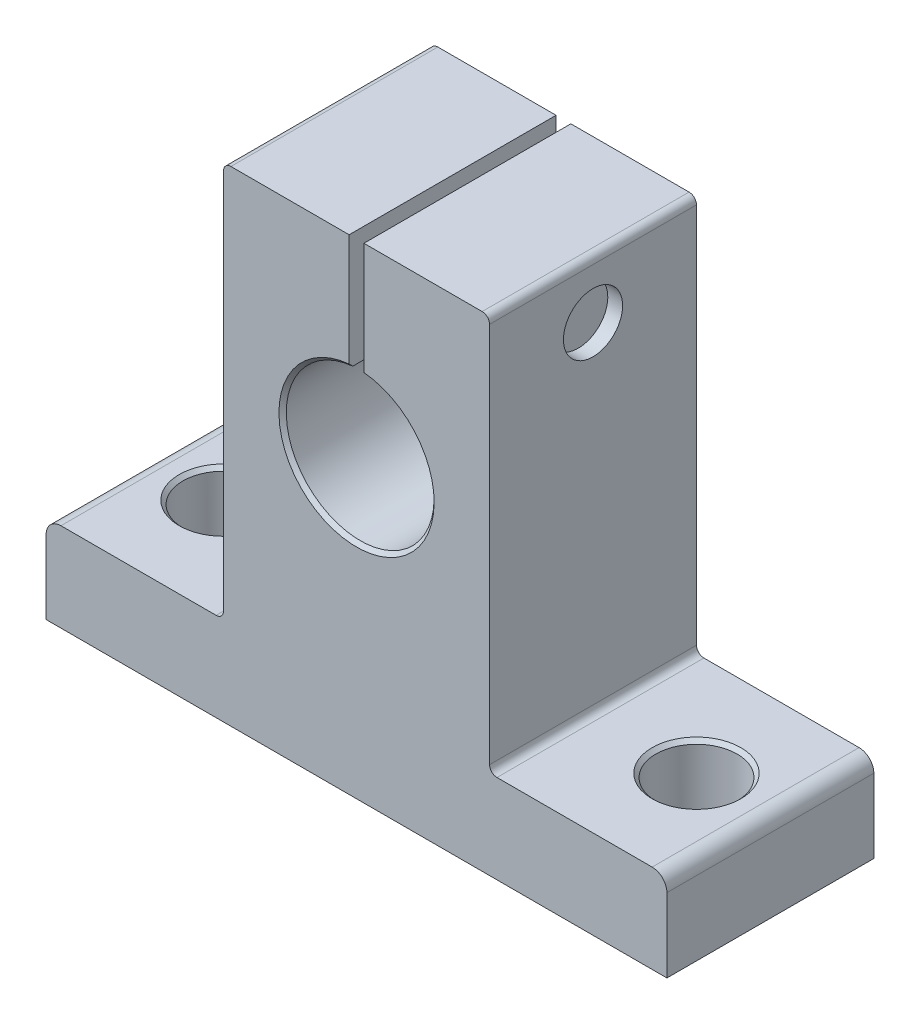
SolidWorks part; units mm, degrees
ref_plane "Front Plane" through (0, 0, 0) normal (0, 0, 1) x (1, 0, 0)
ref_plane "Top Plane" through (0, 0, 0) normal (0, 1, 0) x (1, 0, 0)
ref_plane "Right Plane" through (0, 0, 0) normal (1, 0, 0) x (0, 0, -1)
sketch "Sketch1" plane through (0, 0, 0) normal (0, 0, 1) x (1, 0, 0)
  line L0 (-21, 0) -> (21, 0)
  line L1 (-21, 0) -> (-21, 6)
  line L2 (-21, 6) -> (-9, 6)
  line L3 (-9, 6) -> (-9, 32.8)
  line L4 (-9, 32.8) -> (-0.5, 32.8)
  line L5 (9, 32.8) -> (9, 6)
  line L6 (9, 6) -> (21, 6)
  line L7 (21, 6) -> (21, 0)
  line L8 (-0.5, 32.8) -> (-0.5, 24.9749)
  line L9 (0.5, 32.8) -> (0.5, 24.9749)
  line L10 (0.5, 32.8) -> (9, 32.8)
  arc A0 (-0.5, 24.9749) -> (0.5, 24.9749) centre (0, 20) ccw
  point P11 (0, 0)
  point P13 (-0.5, 28.8875)
  dimension "D6" = 5
  dimension "D1" = 42
  dimension "D2" = 6
  dimension "D3" = 20
  dimension "D4" = 32.8
  dimension "D5" = 1
  dimension "D7" = 18
extrude "Boss-Extrude1" add sketch "Sketch1" along normal blind 14
sketch "Sketch3" plane through (0, 0, 0) normal (0, -1, 0) x (1, 0, 0)
  line L0 (-16, 7) -> (16, 7) construction
  line L1 (-21, 14) -> (-21, 0) construction
  circle A0 centre (-16, 7) radius 2.75
  circle A1 centre (16, 7) radius 2.75
  point P2 (0, 7)
  point P7 (-21, 7)
  dimension "D2" = 5.5
  dimension "D1" = 32
extrude "Cut-Extrude1" cut sketch "Sketch3" against normal blind 6 and the other way through all
fillet "Fillet1" radius 1 2 edges at (21, 6, 7) (-21, 6, 7)
fillet "Fillet2" radius 0.5 4 edges at (-9, 32.8, 7) (9, 32.8, 7) (9, 6, 7) (-9, 6, 7)
chamfer "Chamfer1" distance 0.25 6 edges at (-16, 0, 9.75) (16, 0, 9.75) (18.75, 6, 7) (-13.25, 6, 7) (0, 15, 0) (0, 15, 14)
sketch "Sketch4" plane through (-9, 0, 0) normal (-1, 0, 0) x (0, 0, 1)
  line L0 (14, 32.3) -> (0, 32.3) construction
  line L1 (0, 32.8) -> (14, 32.8) construction
  circle A0 centre (7, 28.9) radius 3.1
  point P6 (7, 32.3)
  dimension "D1" = 6.2
  dimension "D2" = 3.9
extrude "Cut-Extrude2" cut sketch "Sketch4" against normal blind 1
sketch "Sketch5" plane through (-8, 0, 0) normal (-1, 0, 0) x (0, 0, 1)
  circle A0 centre (7, 28.9) radius 3.1
  circle A1 centre (7, 28.9) radius 3
  dimension "D1" = 6
  dimension "D2" = 6.2
extrude "Cut-Extrude3" cut sketch "Sketch5" against normal blind 4
chamfer "Chamfer2" distance 0.2 1 edges at (-8, 25.9, 7)
sketch "Sketch6" plane through (-8, 0, 0) normal (-1, 0, 0) x (0, 0, 1)
  line L1 (7.2255, 30.6173) -> (5.6255, 29.9539)
  line L2 (5.6255, 29.9539) -> (5.4, 28.2366)
  line L3 (5.4, 28.2366) -> (6.7745, 27.1827)
  line L4 (6.7745, 27.1827) -> (8.3745, 27.8461)
  line L5 (8.3745, 27.8461) -> (8.6, 29.5634)
  line L6 (8.6, 29.5634) -> (7.2255, 30.6173)
  circle A0 centre (7, 28.9) radius 1.5 construction
  dimension "D1" = 3
extrude "Cut-Extrude4" cut sketch "Sketch6" against normal blind 2
sketch "Sketch7" plane through (-0.5, 0, 0) normal (1, 0, 0) x (0, 0, -1)
  circle A0 centre (-7, 28.9) radius 2
  dimension "D1" = 4
extrude "Boss-Extrude2" add sketch "Sketch7" along normal blind 1
sketch "Sketch8" plane through (9, 0, 0) normal (1, 0, 0) x (0, 0, -1)
  circle A0 centre (-7, 28.9) radius 2
  dimension "D1" = 4
extrude "Cut-Extrude5" cut sketch "Sketch8" against normal blind 1
sketch "Sketch9" plane through (-8, 0, 0) normal (-1, 0, 0) x (0, 0, 1)
  circle A0 centre (7, 28.9) radius 1.7321
extrude "Cut-Extrude6" cut sketch "Sketch9" against normal blind 1 draft 45
equation "\"h\"= 20'6"
equation "\"w\"= 42'1"
equation "\"l\"= 14'3"
equation "\"f\"= 32.8'2"
equation "\"g\"= 6'9"
equation "\"p\"= 18'5"
equation "\"b\"= 32'4"
equation "\"s\"= 5.5'10"
equation "\"sk\"= 10'7 dg kinh truc"
equation "\"D1@Sketch1\"=\"w\""
equation "\"D2@Sketch1\"=\"g\""
equation "\"D3@Sketch1\"=\"h\""
equation "\"D4@Sketch1\"=\"f\""
equation "\"rk\"= 1'11 be rong khe"
equation "\"D5@Sketch1\"=\"rk\""
equation "\"D6@Sketch1\"=\"sk\"/2"
equation "\"D1@Boss-Extrude1\"=\"l\""
equation "\"D1@Sketch3\"=\"b\""
equation "\"D2@Sketch3\"=\"s\""
equation "\"D1@Cut-Extrude1\"=\"g\""
equation "\"D7@Sketch1\"=\"p\""
equation "\"bo\"= 1'12 bo goc"
equation "\"D1@Fillet1\"=\"bo\""
equation "\"D1@Fillet2\"=\"bo\"/2"
equation "\"D1@Chamfer1\"=\"bo\"/4"
equation "\"m\"= 4'8 bu long"
equation "\"D1@Sketch4\"=1.5*\"m\"+0.2"
equation "\"D1@Sketch5\"=\"m\"*1.5"
equation "\"D2@Sketch5\"=\"m\"*1.5+0.2"
equation "\"D1@Cut-Extrude3\"=\"m\""
equation "\"D1@Chamfer2\"=\"m\"*0.05"
equation "\"D1@Cut-Extrude4\"=\"m\"/2"
equation "\"D1@Sketch6\"=\"m\"*3/4"
equation "\"D1@Sketch7\"=\"m\""
equation "\"D1@Boss-Extrude2\"=\"rk\""
equation "\"D1@Sketch8\"=\"m\""
equation "\"D2@Sketch4\"=(\"f\"-\"h\"-\"sk\"/2)/2"
